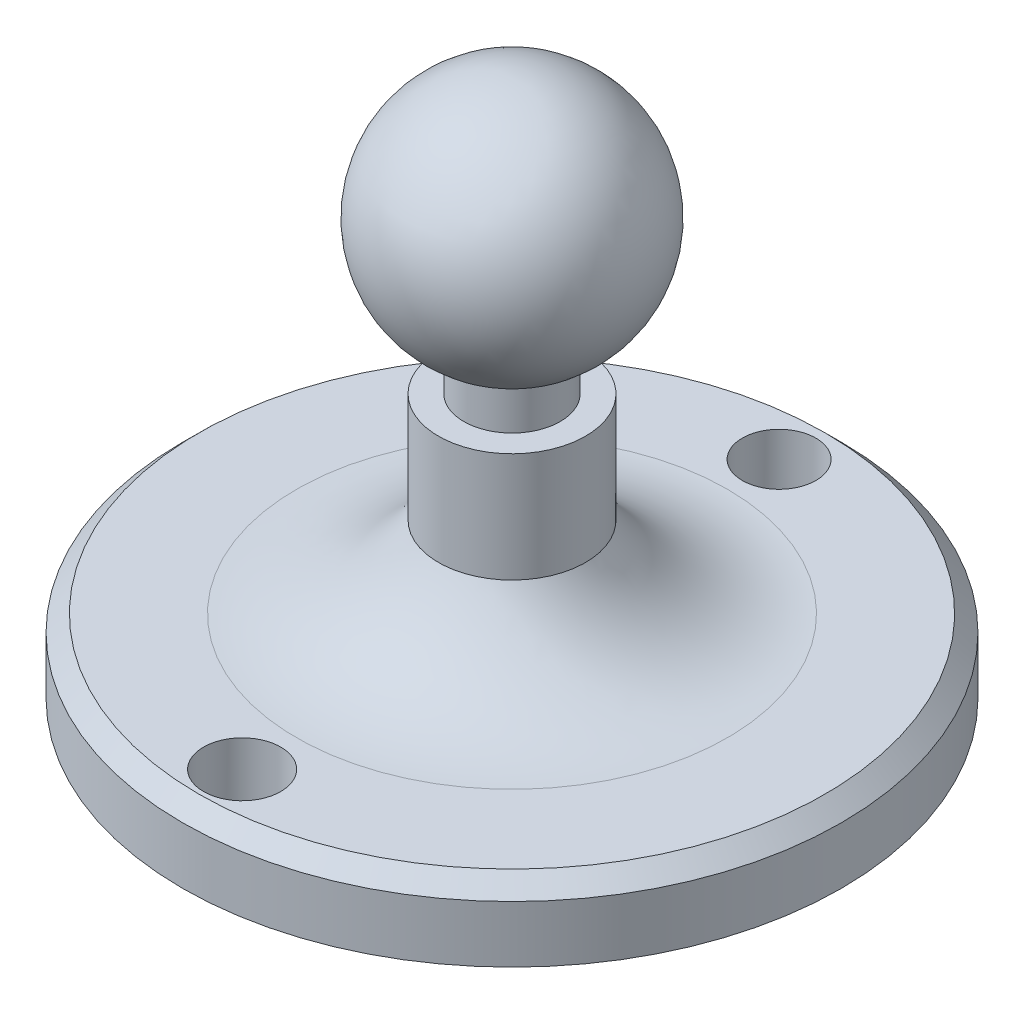
SolidWorks part; units mm, degrees
ref_plane "Alzado" through (0, 0, 0) normal (0, 0, 1) x (1, 0, 0)
ref_plane "Planta" through (0, 0, 0) normal (0, 1, 0) x (1, 0, 0)
ref_plane "Vista lateral" through (0, 0, 0) normal (1, 0, 0) x (0, 0, -1)
sketch "Croquis1" plane through (0, 0, 0) normal (1, 0, 0) x (0, 0, -1)
  line L0 (0, 0) -> (0, 80) construction
  line L1 (0, 0) -> (100, 0)
  line L2 (100, 0) -> (100, 22.2446)
  line L3 (100, 22.2446) -> (65.3581, 22.2446)
  line L4 (22.32, 46.801) -> (22.32, 80)
  line L5 (22.32, 80) -> (14.6298, 80)
  line L6 (0, 0) -> (0, 80) construction
  line L7 (14.6298, 80) -> (14.6298, 92.5206)
  line L8 (0, 80) -> (0, 162.9423) construction
  line L9 (0, 0) -> (0, 162.9423)
  arc A0 (65.3581, 22.2446) -> (22.32, 46.801) centre (65.3581, 72.2374) cw
  arc A1 (14.6298, 92.5206) -> (0, 162.9423) centre (0, 126.2118) ccw
  dimension "D1" = 100
  dimension "D2" = 80
revolve "Revolución1" add sketch "Croquis1" angle 360 about L9
sketch "Croquis2" plane through (0, 22.2446, 0) normal (0, 1, 0) x (1, 0, 0)
  circle A0 centre (0, -81.899) radius 11.7088
  circle A1 centre (0, 81.0547) radius 11.1633
extrude "Cortar-Extruir1" cut sketch "Croquis2" against normal blind 40
chamfer "Chaflán1" distance 5 angle 45 1 edges at (0, 22.2446, -100)
ref_plane "Plano1" through (0, 0, 0) normal (1, 0, 0) x (0, 0, -1)
ref_plane "Plano2" through (0, 0, 0) normal (0, 0, 1) x (1, 0, 0)
